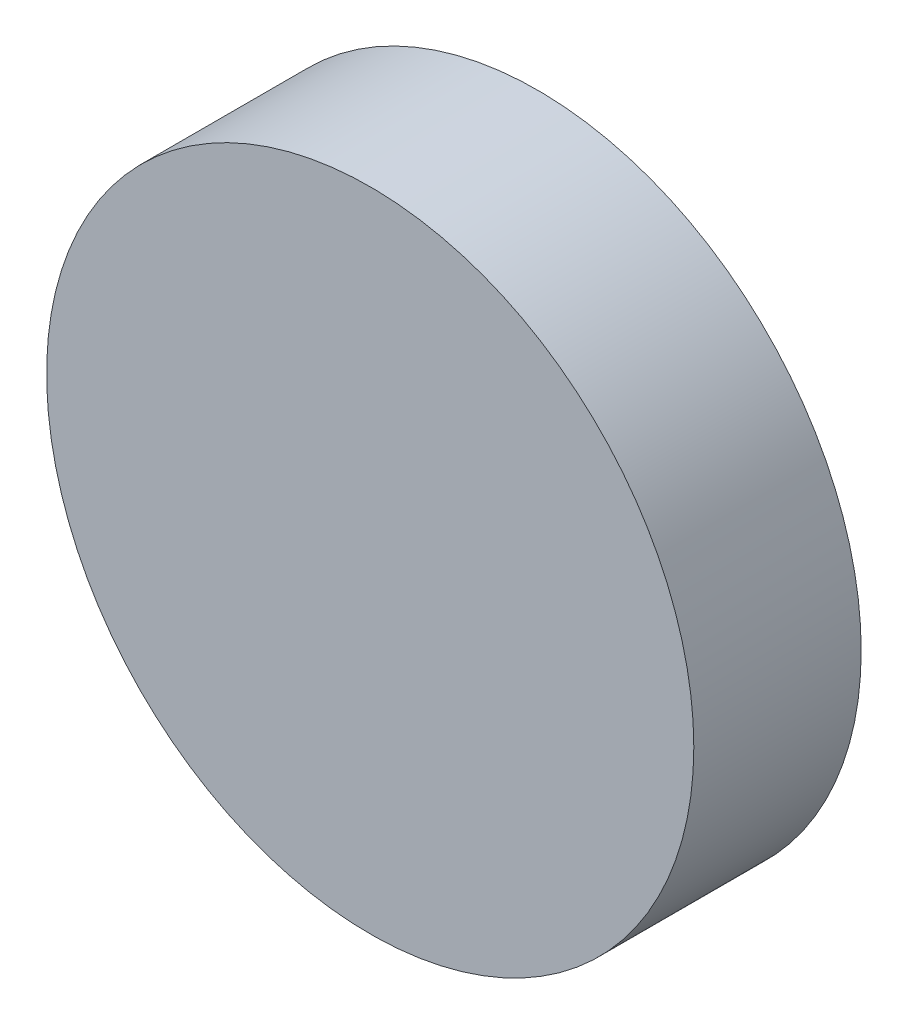
SolidWorks part; units mm, degrees
ref_plane "Front Plane" through (0, 0, 0) normal (0, 0, 1) x (1, 0, 0)
ref_plane "Top Plane" through (0, 0, 0) normal (0, 1, 0) x (1, 0, 0)
ref_plane "Right Plane" through (0, 0, 0) normal (1, 0, 0) x (0, 0, -1)
sketch "Sketch1" plane through (0, 0, 0) normal (0, 0, 1) x (1, 0, 0)
  circle A0 centre (0, 0) radius 29
extrude "Boss-Extrude1" add sketch "Sketch1" along normal blind 15 contours A0
